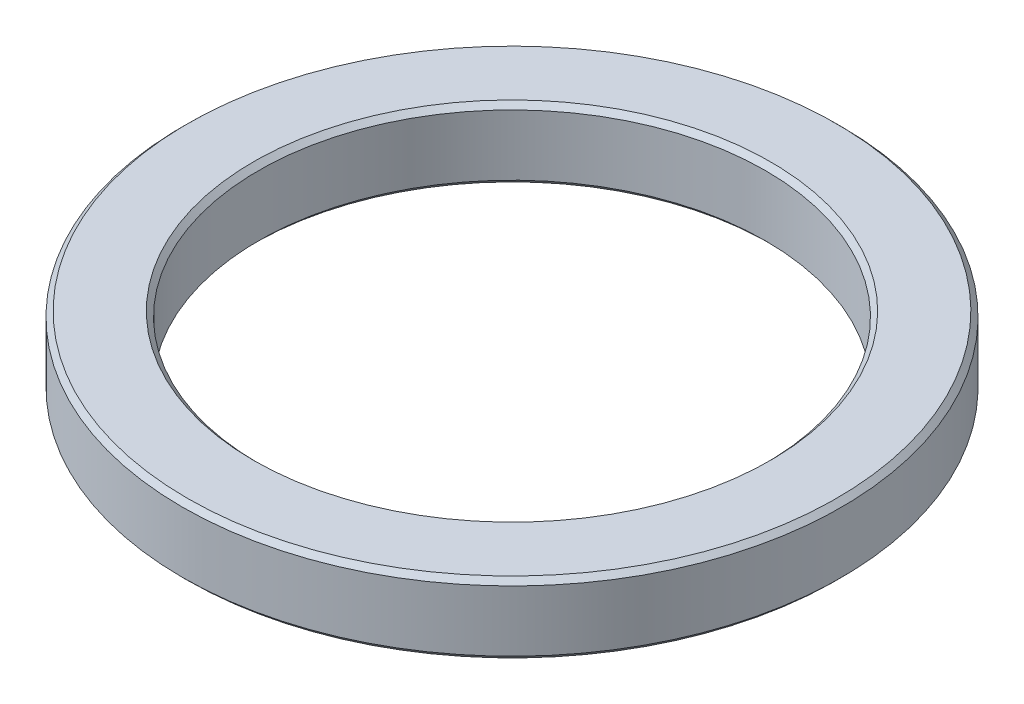
SolidWorks part; units mm, degrees
ref_plane "前视基准面" through (0, 0, 0) normal (0, 0, 1) x (1, 0, 0)
ref_plane "上视基准面" through (0, 0, 0) normal (0, 1, 0) x (1, 0, 0)
ref_plane "右视基准面" through (0, 0, 0) normal (1, 0, 0) x (0, 0, -1)
sketch "草图1" plane through (0, 0, 0) normal (0, 1, 0) x (1, 0, 0)
  circle A0 centre (0, 0) radius 32.5
  circle A1 centre (0, 0) radius 25
  dimension "D1" = 65
  dimension "D2" = 50
extrude "凸台-拉伸1" add sketch "草图1" along normal blind 7
chamfer "倒角1" distance 0.5 angle 45 4 edges at (0, 0, 25) (0, 0, 32.5) (0, 7, 25) (0, 7, 32.5)
